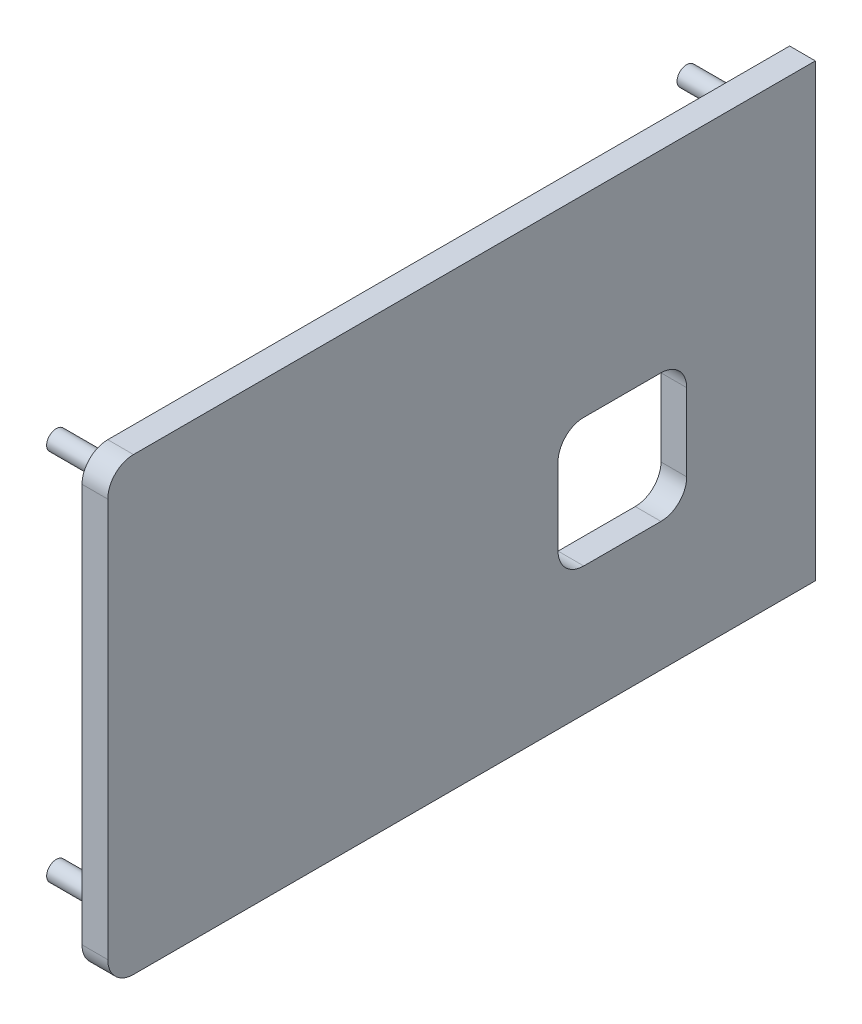
SolidWorks part; units mm, degrees
ref_plane "Front Plane" through (0, 0, 0) normal (0, 0, 1) x (1, 0, 0)
ref_plane "Top Plane" through (0, 0, 0) normal (0, 1, 0) x (1, 0, 0)
ref_plane "Right Plane" through (0, 0, 0) normal (1, 0, 0) x (0, 0, -1)
sketch "Sketch2" plane through (0, 0, 0) normal (1, 0, 0) x (0, 0, -1)
  line L1 (-69.7357, 48.6803) -> (69.9643, 48.6803)
  line L2 (-69.7357, 48.6803) -> (-69.7357, -40.2197)
  line L3 (-69.7357, -40.2197) -> (69.9643, -40.2197)
  line L4 (69.9643, 48.6803) -> (69.9643, -40.2197)
  line L5 (-69.7357, 48.6803) -> (69.9643, -40.2197) construction
  line L6 (-69.7357, -40.2197) -> (69.9643, 48.6803) construction
  point P0 (0.1143, 4.2303)
  dimension "D1" = 88.9
  dimension "D2" = 139.7
extrude "Boss-Extrude1" add sketch "Sketch2" along normal blind 5.08
sketch "Sketch3" plane through (0, 0, 0) normal (-1, 0, 0) x (0, 0, 1)
  line L4 (-69.9643, 48.6803) -> (-69.9643, -40.2197)
  line L5 (-69.9643, -40.2197) -> (69.7357, -40.2197)
  line L6 (69.7357, -40.2197) -> (69.7357, 48.6803)
  line L7 (69.7357, 48.6803) -> (-69.9643, 48.6803)
  line L8 (-69.9643, 48.6803) -> (-69.9643, -40.2197)
  line L9 (-69.9643, -40.2197) -> (69.7357, -40.2197)
  line L10 (69.7357, -40.2197) -> (69.7357, 48.6803)
  line L11 (69.7357, 48.6803) -> (-69.9643, 48.6803)
  line L16 (-64.8843, 43.6003) -> (-64.8843, -35.1397)
  line L17 (-64.8843, -35.1397) -> (64.6557, -35.1397)
  line L18 (64.6557, -35.1397) -> (64.6557, 43.6003)
  line L19 (64.6557, 43.6003) -> (-64.8843, 43.6003)
  line L20 (-64.8843, 43.6003) -> (-64.8843, -35.1397)
  line L21 (-64.8843, -35.1397) -> (64.6557, -35.1397)
  line L22 (64.6557, -35.1397) -> (64.6557, 43.6003)
  line L23 (64.6557, 43.6003) -> (-64.8843, 43.6003)
  circle A0 centre (-62.3443, 41.0603) radius 1.905
  circle A1 centre (-62.3443, -32.5997) radius 1.905
  circle A2 centre (62.1157, 41.0603) radius 1.905
  circle A3 centre (62.1157, -32.5997) radius 1.905
  dimension "D3" = 3.81
  dimension "D4" = 3.81
  dimension "D5" = 3.81
  dimension "D6" = 3.81
  dimension "D7" = 2.54
  dimension "D8" = 2.54
  dimension "D9" = 2.54
  dimension "D10" = 2.54
  dimension "D11" = 2.54
  dimension "D12" = 2.54
  dimension "D13" = 2.54
  dimension "D14" = 2.54
  dimension "D1" = 0
  dimension "D2" = 5.08
extrude "Boss-Extrude2" add sketch "Sketch3" along normal blind 12.7 contours A0 | A1 | A2 | A3
fillet "Fillet1" radius 5.08 2 edges at (2.54, 48.6803, 69.7357) (2.54, -40.2197, 69.7357)
sketch "Sketch4" plane through (5.08, 0, 0) normal (1, 0, 0) x (0, 0, -1)
  line L1 (44.5643, -14.8197) -> (19.1643, -14.8197)
  line L2 (44.5643, -14.8197) -> (44.5643, 10.5803)
  line L3 (44.5643, 10.5803) -> (19.1643, 10.5803)
  line L4 (19.1643, -14.8197) -> (19.1643, 10.5803)
  line L5 (69.9643, 48.6803) -> (-64.6557, 48.6803) construction
  line L6 (69.9643, -40.2197) -> (69.9643, 48.6803) construction
  dimension "D1" = 38.1
  dimension "D2" = 25.4
  dimension "D3" = 25.4
  dimension "D4" = 25.4
extrude "Cut-Extrude1" cut sketch "Sketch4" against normal blind 5.08
fillet "Fillet2" radius 5.08 4 edges at (2.54, 10.5803, -44.5643) (2.54, -14.8197, -44.5643) (2.54, -14.8197, -19.1643) (2.54, 10.5803, -19.1643)
